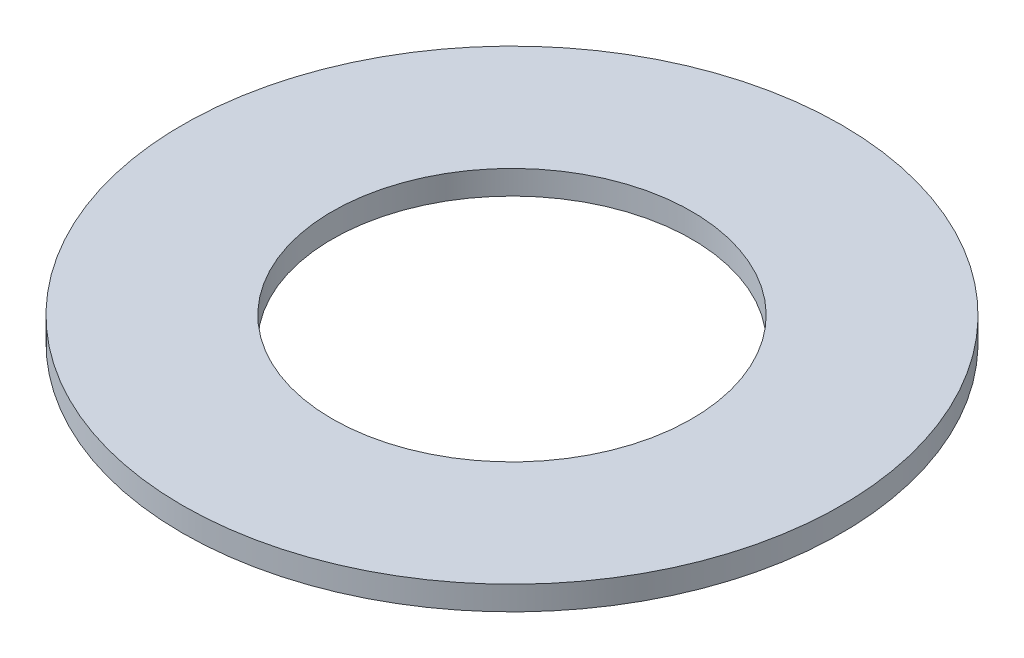
SolidWorks part; units mm, degrees
ref_plane "Front Plane" through (0, 0, 0) normal (0, 0, 1) x (1, 0, 0)
ref_plane "Top Plane" through (0, 0, 0) normal (0, 1, 0) x (1, 0, 0)
ref_plane "Right Plane" through (0, 0, 0) normal (1, 0, 0) x (0, 0, -1)
sketch "Sketch1" plane through (0, 0, 0) normal (0, 1, 0) x (1, 0, 0)
  circle A0 centre (0, 0) radius 15
  circle A1 centre (0, 0) radius 27.5
  point P5 (0, -0.4893)
  dimension "D1" = 30
  dimension "D2" = 55
extrude "Boss-Extrude1" add sketch "Sketch1" along normal blind 2
